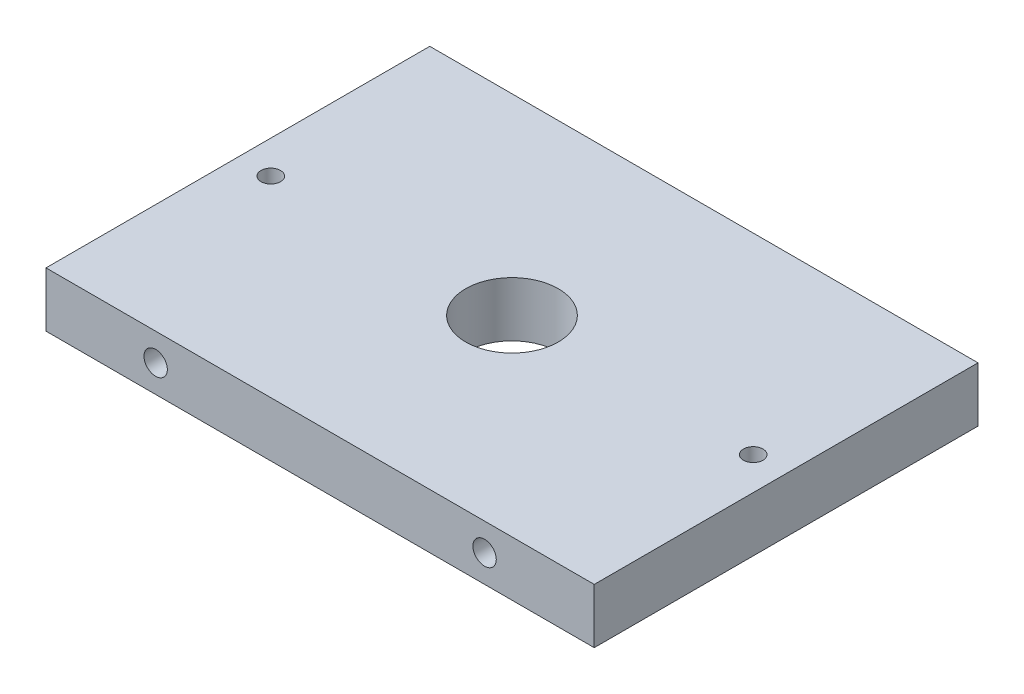
SolidWorks part; units mm, degrees
ref_plane "Front Plane" through (0, 0, 0) normal (0, 0, 1) x (1, 0, 0)
ref_plane "Top Plane" through (0, 0, 0) normal (0, 1, 0) x (1, 0, 0)
ref_plane "Right Plane" through (0, 0, 0) normal (1, 0, 0) x (0, 0, -1)
sketch "Sketch1" plane through (0, 0, 0) normal (0, 1, 0) x (1, 0, 0)
  line L1 (-26.9974, 3.2608) -> (36.5026, 3.2608)
  line L2 (-26.9974, 3.2608) -> (-26.9974, -41.1892)
  line L3 (-26.9974, -41.1892) -> (36.5026, -41.1892)
  line L4 (36.5026, 3.2608) -> (36.5026, -41.1892)
  dimension "D1" = 44.45
  dimension "D2" = 63.5
extrude "Boss-Extrude1" add sketch "Sketch1" along normal blind 6.35
hole_wizard "Ø3.0 (3) Diameter Hole5" positions "Sketch15" profile "Sketch14" hole size "Ø3.0" standard "Ansi Metric"
sketch "Sketch15" plane through (-26.9974, 0, 0) normal (-1, 0, 0) x (0, 0, 1)
  line L0 (-22.3108, 6.35) -> (-22.3108, 0) construction
  line L1 (-22.3108, 6.35) -> (41.1892, 6.35) construction
  point P0 (-9.6108, 3.175)
  point P1 (28.4892, 3.175)
  dimension "D1" = 38.1
  dimension "D2" = 3.175
  dimension "D3" = 3.175
  dimension "D4" = 3.175
sketch "Sketch14" plane through (-26.9974, 3.175, -9.6108) normal (0, 1, 0) x (0, 0, 1)
  line L0 (0, 0) -> (0, 13.6013)
  line L1 (0, 13.6013) -> (1.5, 12.7)
  line L2 (1.5, 12.7) -> (1.5, 0)
  line L5 (1.5, 0) -> (0, 0)
  line L10 (0, 13.6013) -> (-1.5, 12.7) construction
  line L11 (0, -6.35) -> (0, 107.95) construction
  dimension "Hole Dia." = 3
  dimension "Hole Depth" = 12.7
  dimension "Drill Angle" = 118
hole_wizard "Tap Drill for #4-40 Tap1" positions "Sketch17" profile "Sketch16" hole size "#4-40" standard "Ansi Inch"
sketch "Sketch17" plane through (0, 0, 0) normal (0, -1, 0) x (1, 0, 0)
  line L0 (-26.9974, 41.1892) -> (36.5026, 41.1892) construction
  line L1 (-26.9974, -3.2608) -> (-26.9974, 41.1892) construction
  point P0 (-23.1874, 18.9642)
  dimension "D1" = 22.225
  dimension "D2" = 3.81
sketch "Sketch16" plane through (-23.1874, 0, 18.9642) normal (1, 0, 0) x (0, 0, -1)
  line L0 (0, 0) -> (0, 13.3792)
  line L1 (0, 13.3792) -> (1.1303, 12.7)
  line L2 (1.1303, 12.7) -> (1.1303, 0)
  line L5 (1.1303, 0) -> (0, 0)
  line L10 (0, 13.3792) -> (-1.1303, 12.7) construction
  line L11 (0, -6.35) -> (0, 107.95) construction
  dimension "Hole Dia." = 2.2606
  dimension "Hole Depth" = 12.7
  dimension "Drill Angle" = 118
pattern_linear "LPattern1" count 2 spacing 55.88 along (1, 0, 0) of "Tap Drill for #4-40 Tap1"
hole_wizard "Tap Drill for #6-32 Tap1" positions "Sketch23" profile "Sketch22" hole size "#6-32" standard "Ansi Inch"
sketch "Sketch23" plane through (0, 0, 41.1892) normal (0, 0, 1) x (1, 0, 0)
  line L0 (-26.9974, 6.35) -> (-26.9974, 0) construction
  line L1 (-26.9974, 0) -> (36.5026, 0) construction
  point P0 (23.8026, 3.175)
  point P1 (-14.2974, 3.175)
  dimension "D1" = 38.1
  dimension "D2" = 12.7
  dimension "D3" = 3.175
sketch "Sketch22" plane through (23.8026, 3.175, 41.1892) normal (1, 0, 0) x (0, -1, 0)
  line L0 (0, 0) -> (0, 7.1627)
  line L1 (0, 7.1627) -> (1.3525, 6.35)
  line L2 (1.3525, 6.35) -> (1.3525, 0)
  line L5 (1.3525, 0) -> (0, 0)
  line L10 (0, 7.1627) -> (-1.3526, 6.35) construction
  line L11 (0, -6.35) -> (0, 107.95) construction
  dimension "Hole Dia." = 2.7051
  dimension "Hole Depth" = 6.35
  dimension "Drill Angle" = 118
hole_wizard "Tap Drill for #6-32 Tap2" positions "Sketch25" profile "Sketch24" hole size "#6-32" standard "Ansi Inch"
sketch "Sketch25" plane through (0, 0, -3.2608) normal (0, 0, -1) x (-1, 0, 0)
  line L0 (-36.5026, 0) -> (26.9974, 0) construction
  line L1 (26.9974, 6.35) -> (26.9974, 0) construction
  point P0 (14.2974, 3.175)
  point P1 (-23.8026, 3.175)
  dimension "D1" = 38.1
  dimension "D2" = 3.175
  dimension "D3" = 12.7
sketch "Sketch24" plane through (-14.2974, 3.175, -3.2608) normal (1, 0, 0) x (0, 1, 0)
  line L0 (0, 0) -> (0, 7.1627)
  line L1 (0, 7.1627) -> (1.3525, 6.35)
  line L2 (1.3525, 6.35) -> (1.3525, 0)
  line L5 (1.3525, 0) -> (0, 0)
  line L10 (0, 7.1627) -> (-1.3526, 6.35) construction
  line L11 (0, -6.35) -> (0, 107.95) construction
  dimension "Hole Dia." = 2.7051
  dimension "Hole Depth" = 6.35
  dimension "Drill Angle" = 118
hole_wizard "Tap Drill for 1/2-13 Tap1" positions "Sketch27" profile "Sketch26" hole size "1/2-13" standard "Ansi Inch"
sketch "Sketch27" plane through (0, 6.35, 0) normal (0, 1, 0) x (-1, 0, 0)
  line L0 (26.9974, -3.2608) -> (26.9974, 41.1892) construction
  line L1 (26.9974, 41.1892) -> (-36.5026, 41.1892) construction
  point P0 (-4.7526, 18.9642)
  dimension "D1" = 31.75
  dimension "D2" = 22.225
sketch "Sketch26" plane through (4.7526, 6.35, 18.9642) normal (1, 0, 0) x (0, 0, 1)
  line L0 (0, 0) -> (0, 9.5695)
  line L1 (0, 9.5695) -> (5.3581, 6.35)
  line L2 (5.3581, 6.35) -> (5.3581, 0)
  line L5 (5.3581, 0) -> (0, 0)
  line L10 (0, 9.5695) -> (-5.3581, 6.35) construction
  line L11 (0, -6.35) -> (0, 107.95) construction
  dimension "Hole Dia." = 10.7163
  dimension "Hole Depth" = 6.35
  dimension "Drill Angle" = 118
equation "\"D2@Sketch15\" = (\"D1@Sketch1\"-\"D1@Sketch15\")/2"
equation "\"D3@Sketch15\" = \"RD1@Annotations\"/2"
equation "\"D1@Sketch27\" = \"D2@Sketch1\"/2"
equation "\"D2@Sketch23\" = (\"D2@Sketch1\"-\"D1@Sketch23\")/2"
equation "\"D3@Sketch23\" = \"RD1@Annotations\"/2"
equation "\"D3@Sketch25\" = (\"D2@Sketch1\"-\"D1@Sketch25\")/2"
equation "\"D1@Sketch17\" = \"D1@Sketch1\"/2"
equation "\"D2@Sketch17\" = (\"D2@Sketch1\"-\"RD2@Annotations\")/2"
equation "\"D2@Sketch27\" = \"D1@Sketch1\"/2"
